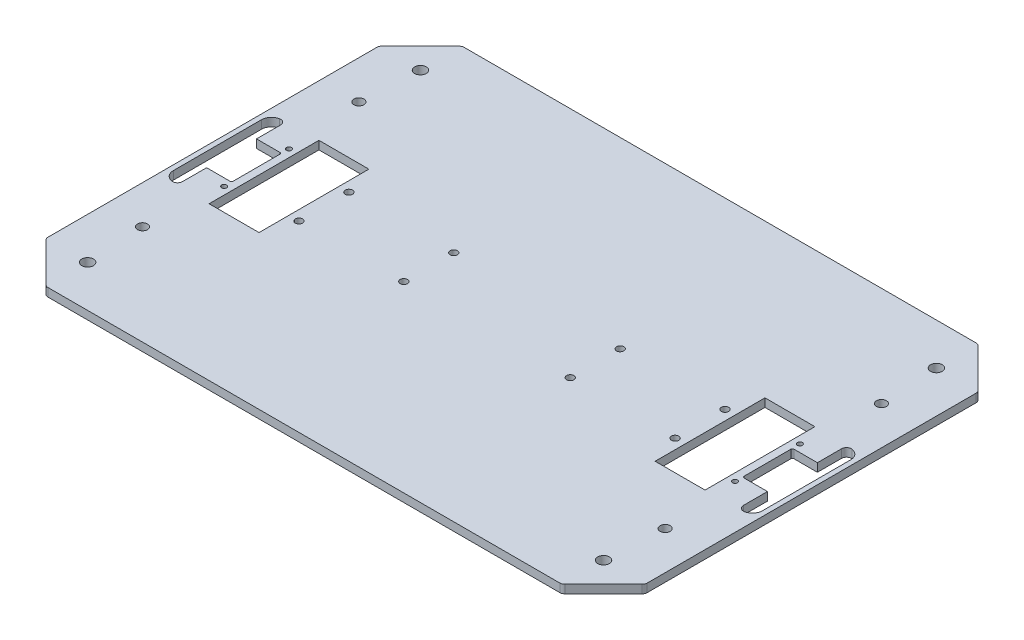
SolidWorks part; units mm, degrees
ref_plane "Plan de face" through (0, 0, 0) normal (0, 0, 1) x (1, 0, 0)
ref_plane "Plan de dessus" through (0, 0, 0) normal (0, 1, 0) x (1, 0, 0)
ref_plane "Plan de droite" through (0, 0, 0) normal (1, 0, 0) x (0, 0, -1)
sketch "Esquisse1" plane through (0, 0, 0) normal (0, 1, 0) x (1, 0, 0)
  line L0 (0, 125) -> (0, -125) construction
  line L1 (-180, 0) -> (180, 0) construction
  line L2 (-155, 125) -> (155, 125)
  line L3 (-155, -125) -> (155, -125)
  line L4 (-180, 100) -> (-180, -100)
  line L5 (180, 100) -> (180, -100)
  line L6 (-180, 100) -> (-155, 125)
  line L7 (-180, -100) -> (-155, -125)
  line L8 (155, -125) -> (180, -100)
  line L9 (155, 125) -> (180, 100)
  point P4 (0, 0)
  point P8 (0, 0)
  point P10 (0, 125)
  point P14 (0, -125)
  point P17 (-180, 0)
  point P20 (180, 0)
  dimension "D1" = 360
  dimension "D2" = 250
  dimension "D3" = 135
  dimension "D4" = 310
  dimension "D5" = 200
extrude "Boss.-Extru.1" add sketch "Esquisse1" along normal blind 5
fillet "Congé1" radius 3 8 edges at (-180, 2.5, 100) (-155, 2.5, 125) (155, 2.5, 125) (180, 2.5, 100) (180, 2.5, -100) (155, 2.5, -125) (-155, 2.5, -125) (-180, 2.5, -100)
sketch "Esquisse2" plane through (0, 5, 0) normal (0, 1, 0) x (1, 0, 0)
  line L0 (180, 0) -> (-180, 0) construction
  line L1 (-180, 98.7574) -> (-180, -98.7574) construction
  line L2 (-157, 0) -> (-157, -65) construction
  line L3 (-157, -65) -> (-180, -65) construction
  line L4 (0, 125) -> (0, -125) construction
  line L5 (-153.7574, -125) -> (153.7574, -125) construction
  circle A0 centre (-157, -65) radius 3
  circle A1 centre (-157, 65) radius 3
  circle A2 centre (157, -65) radius 3
  circle A3 centre (157, 65) radius 3
  point P6 (0, 0)
  point P18 (0, 0)
  dimension "D3" = 6
  dimension "D1" = 23
  dimension "D2" = 65
extrude "Perçage Profilé" cut sketch "Esquisse2" against normal through all
sketch "Esquisse3" plane through (0, 5, 0) normal (0, 1, 0) x (1, 0, 0)
  line L0 (-153.5, 19.5) -> (-153.5, -19.5) construction
  line L1 (180, 0) -> (-180, 0) construction
  line L2 (-180, 98.7574) -> (-180, -98.7574) construction
  line L3 (0, 125) -> (0, -125) construction
  line L4 (-153.7574, -125) -> (153.7574, -125) construction
  circle A0 centre (-153.5, 19.5) radius 1.5
  circle A1 centre (-153.5, -19.5) radius 1.5
  circle A2 centre (153.5, -19.5) radius 1.5
  circle A3 centre (153.5, 19.5) radius 1.5
  point P4 (-153.5, 0)
  point P10 (0, 0)
  point P16 (0, 0)
  dimension "D2" = 3
  dimension "D1" = 39
  dimension "D3" = 26.5
extrude "Perçage Encodeur" cut sketch "Esquisse3" against normal through all
sketch "Esquisse4" plane through (0, 5, 0) normal (0, 1, 0) x (1, 0, 0)
  line L0 (180, 0) -> (-180, 0) construction
  line L1 (168.5, -15) -> (154.5, -15)
  line L2 (-153.5, -14) -> (-153.5, 14)
  line L4 (-154.5, 15) -> (-168.5, 15)
  line L5 (-168.5, 15) -> (-168.5, 32.5)
  line L6 (-168.5, 32.5) -> (-177, 32.5)
  line L7 (-177, 32.5) -> (-177, -32.5)
  line L8 (-177, -32.5) -> (-168.5, -32.5)
  line L9 (-168.5, -32.5) -> (-168.5, -15)
  line L10 (-168.5, -15) -> (-154.5, -15)
  line L12 (-168.5, 15) -> (-168.5, -15) construction
  line L13 (168.5, -32.5) -> (168.5, -15)
  line L14 (0, 125) -> (0, -125) construction
  line L15 (-153.7574, -125) -> (153.7574, -125) construction
  line L16 (177, -32.5) -> (168.5, -32.5)
  line L27 (-180, 98.7574) -> (-180, -98.7574) construction
  line L28 (177, 32.5) -> (177, -32.5)
  line L29 (168.5, 32.5) -> (177, 32.5)
  line L30 (168.5, 15) -> (168.5, 32.5)
  line L31 (154.5, 15) -> (168.5, 15)
  line L32 (153.5, -14) -> (153.5, 14)
  arc A0 (-153.5, -14) -> (-154.5, -15) centre (-154.5, -14) cw
  arc A1 (-153.5, 14) -> (-154.5, 15) centre (-154.5, 14) ccw
  arc A2 (153.5, 14) -> (154.5, 15) centre (154.5, 14) cw
  arc A3 (153.5, -14) -> (154.5, -15) centre (154.5, -14) ccw
  point P6 (0, 0)
  point P10 (-153.5, 0)
  point P19 (-168.5, 0)
  point P25 (0, 0)
  point P28 (-153.5, 15)
  point P32 (-177, 0)
  point P45 (153.5, 15)
  point P46 (153.5, 0)
  dimension "D2" = 1
  dimension "D1" = 15
  dimension "D3" = 8.5
  dimension "D4" = 65
  dimension "D5" = 30
  dimension "D6" = 3
extrude "Poche Roue Encodeuse" cut sketch "Esquisse4" against normal through all
fillet "Congé2" radius 6 4 edges at (177, 2.5, 32.5) (177, 2.5, -32.5) (-177, 2.5, 32.5) (-177, 2.5, -32.5)
fillet "Congé3" radius 3 4 edges at (168.5, 2.5, 32.5) (168.5, 2.5, -32.5) (-168.5, 2.5, 32.5) (-168.5, 2.5, -32.5)
sketch "Esquisse5" plane through (0, 5, 0) normal (0, 1, 0) x (1, 0, 0)
  line L0 (0, 125) -> (0, -125) construction
  line L1 (153.7574, 125) -> (-153.7574, 125) construction
  line L2 (-153.7574, -125) -> (153.7574, -125) construction
  line L3 (-180, 0) -> (180, 0) construction
  line L4 (-180, 98.7574) -> (-180, -98.7574) construction
  line L5 (180, -98.7574) -> (180, 98.7574) construction
  line L7 (-50, 15) -> (-113, 15) construction
  line L8 (-50, 15) -> (-50, -15) construction
  line L9 (-50, -15) -> (-113, -15) construction
  line L10 (-113, 15) -> (-113, -15) construction
  circle A0 centre (-113, 15) radius 2.2
  circle A1 centre (-113, -15) radius 2.2
  circle A2 centre (-50, -15) radius 2.2
  circle A3 centre (-50, 15) radius 2.2
  circle A4 centre (50, 15) radius 2.2
  circle A5 centre (50, -15) radius 2.2
  circle A6 centre (113, -15) radius 2.2
  circle A7 centre (113, 15) radius 2.2
  point P16 (-50, 0)
  dimension "D4" = 4.4
  dimension "D1" = 30
  dimension "D2" = 63
  dimension "D3" = 50
extrude "Perçage Bloc Moteur" cut sketch "Esquisse5" against normal through all
sketch "Esquisse6" plane through (0, 5, 0) normal (0, 1, 0) x (1, 0, 0)
  line L0 (-113, 15) -> (-113, -15) construction
  line L1 (-149, 33) -> (-119, 33)
  line L2 (-149, 33) -> (-149, -33)
  line L3 (-149, -33) -> (-119, -33)
  line L4 (-119, 33) -> (-119, -33)
  line L5 (-119, 0) -> (-113, 0) construction
  line L6 (0, 125) -> (0, -125) construction
  line L7 (-153.7574, -125) -> (153.7574, -125) construction
  line L8 (149, -33) -> (119, -33)
  line L9 (119, 33) -> (119, -33)
  line L10 (149, 33) -> (149, -33)
  line L11 (149, 33) -> (119, 33)
  point P16 (0, 0)
  dimension "D1" = 30
  dimension "D2" = 119
  dimension "D3" = 66
extrude "Poche Roue Motrice" cut sketch "Esquisse6" against normal through all
sketch "Esquisse7" plane through (0, 5, 0) normal (0, 1, 0) x (1, 0, 0)
  line L0 (-180, 98.7574) -> (-180, -98.7574) construction
  line L1 (153.7574, 125) -> (-153.7574, 125) construction
  line L2 (0, 125) -> (0, -125) construction
  line L3 (-153.7574, -125) -> (153.7574, -125) construction
  line L4 (-180, 0) -> (180, 0) construction
  line L5 (180, -98.7574) -> (180, 98.7574) construction
  circle A0 centre (-155, 100) radius 3.5
  circle A1 centre (-155, -100) radius 3.5
  circle A2 centre (155, -100) radius 3.5
  circle A3 centre (155, 100) radius 3.5
  point P12 (0, 0)
  point P18 (0, 0)
  dimension "D1" = 7
  dimension "D2" = 25
  dimension "D3" = 25
extrude "Perçage Patin" cut sketch "Esquisse7" against normal through all
